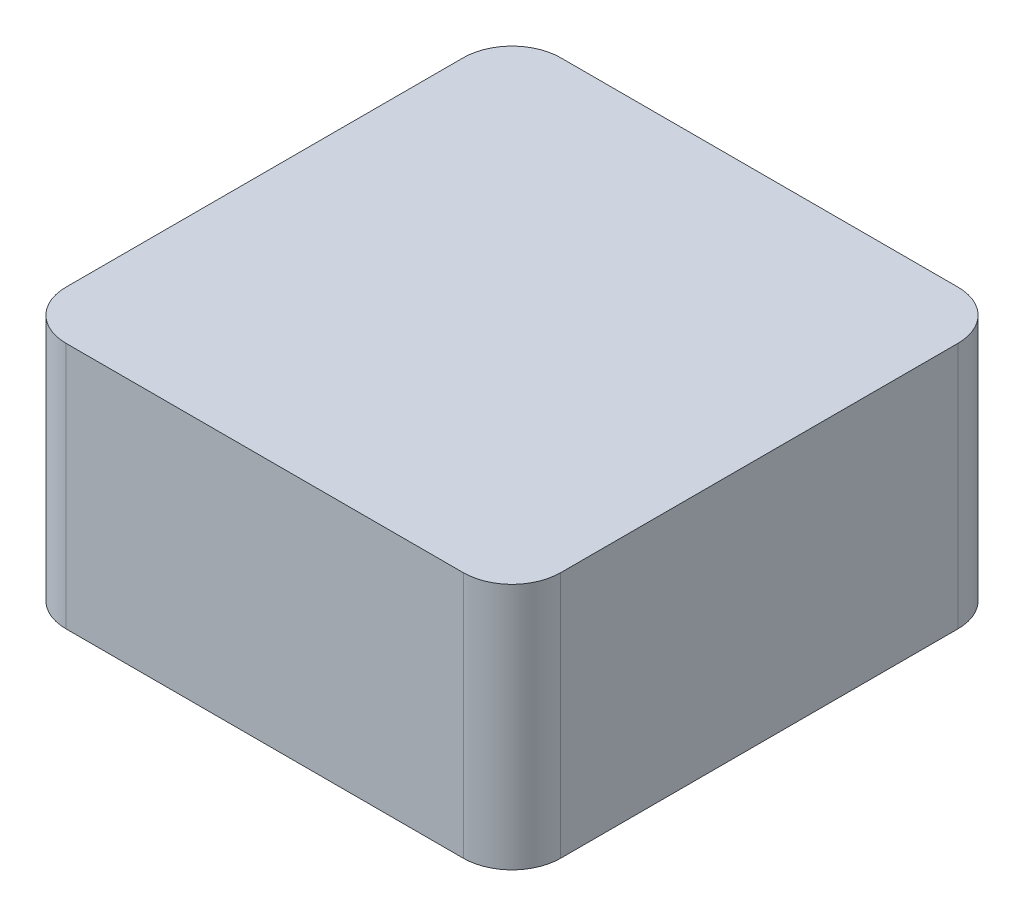
SolidWorks part; units mm, degrees
ref_plane "Front Plane" through (0, 0, 0) normal (0, 0, 1) x (1, 0, 0)
ref_plane "Top Plane" through (0, 0, 0) normal (0, 1, 0) x (1, 0, 0)
ref_plane "Right Plane" through (0, 0, 0) normal (1, 0, 0) x (0, 0, -1)
sketch "Sketch1" plane through (0, 0, 0) normal (0, 0, 1) x (1, 0, 0)
  line L0 (0, 0) -> (203.2, 0)
  line L1 (0, 0) -> (0, 101.6)
  line L2 (203.2, 0) -> (203.2, 101.6)
  line L3 (203.2, 101.6) -> (0, 101.6)
  dimension "D1" = 203.2
  dimension "D2" = 101.6
  dimension "D3" = 101.6
  dimension "D4" = 203.2
extrude "Boss-Extrude2" add sketch "Sketch1" along normal blind 203.2
fillet "Fillet3" radius 20 1 edges at (0, 50.8, 0)
fillet "Fillet4" radius 20 1 edges at (203.2, 50.8, 0)
fillet "Fillet5" radius 20 1 edges at (0, 50.8, 203.2)
fillet "Fillet6" radius 20 1 edges at (203.2, 50.8, 203.2)
sketch "Sketch2" plane through (0, 0, 0) normal (0, -1, 0) x (1, 0, 0)
  line L1 (23.8, 176.2) -> (176.2, 176.2)
  line L2 (23.8, 176.2) -> (23.8, 23.8)
  line L3 (23.8, 23.8) -> (176.2, 23.8)
  line L4 (176.2, 176.2) -> (176.2, 23.8)
  line L5 (23.8, 176.2) -> (176.2, 23.8) construction
  line L6 (23.8, 23.8) -> (176.2, 176.2) construction
  point P0 (100, 100)
  dimension "D1" = 152.4
extrude "Cut-Extrude1" cut sketch "Sketch2" against normal blind 88.9
